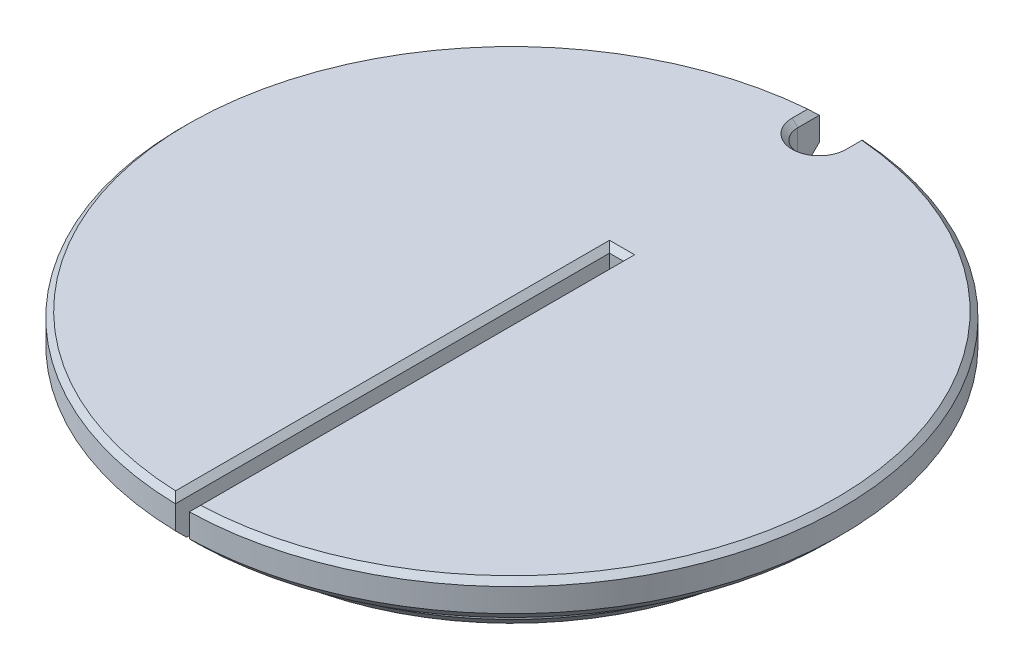
SolidWorks part; units mm, degrees
material "ABS"
ref_plane "Front Plane" through (0, 0, 0) normal (0, 0, 1) x (1, 0, 0)
ref_plane "Top Plane" through (0, 0, 0) normal (0, 1, 0) x (1, 0, 0)
ref_plane "Right Plane" through (0, 0, 0) normal (1, 0, 0) x (0, 0, -1)
sketch "Sketch1" plane through (0, 0, 0) normal (0, 0, 1) x (1, 0, 0)
  line L0 (0, -1000) -> (0, 49000) construction
  line L1 (0, 0) -> (0, -7.62)
  line L2 (0, -7.62) -> (25.0698, -7.62)
  line L3 (25.0698, -7.62) -> (25.0698, -3.6576)
  line L4 (25.0698, -3.6576) -> (30.0228, -3.6576)
  line L5 (30.0228, -3.6576) -> (30.0228, 0)
  line L6 (30.0228, 0) -> (0, 0)
  dimension "D1" = 30.0228
  dimension "D2" = 25.0698
  dimension "D3" = 7.62
  dimension "D4" = 3.6576
revolve "Revolve1" add sketch "Sketch1" angle 360 about L0
sketch "Sketch3" plane through (0, 0, 0) normal (0, 1, 0) x (1, 0, 0)
  line L0 (-0.635, 9.525) -> (0.635, 9.525)
  line L1 (0.635, 9.525) -> (0.635, -30.0161)
  line L2 (-0.635, 9.525) -> (-0.635, -30.0161)
  line L3 (0, -1000) -> (0, 49000) construction
  circle A0 centre (0, 0) radius 30.0228 construction
  arc A1 (-0.635, -30.0161) -> (0.635, -30.0161) centre (0, 0) ccw
  dimension "D1" = 9.525
  dimension "D2" = 1.27
extrude "Cut-Extrude2" cut sketch "Sketch3" against normal through all
sketch "Sketch5" plane through (0, 0, 0) normal (0, 1, 0) x (1, 0, 0)
  line L0 (0, -1000) -> (0, 49000) construction
  line L1 (-1.9558, 29.959) -> (-1.9558, 27.9908)
  line L2 (1.9558, 29.959) -> (1.9558, 27.9908)
  arc A0 (0.635, -30.0161) -> (-0.635, -30.0161) centre (0, 0) ccw construction
  arc A1 (-1.9558, 29.959) -> (1.9558, 29.959) centre (0, 0) cw
  arc A2 (-1.9558, 27.9908) -> (1.9558, 27.9908) centre (0, 27.9908) ccw
  dimension "D1" = 3.9878
  dimension "D2" = 3.9116
extrude "Cut-Extrude3" cut sketch "Sketch5" against normal through all
chamfer "Chamfer1" distance 1.016 angle 45 3 edges at (0, -7.62, -25.0698) (30.0155, -3.6576, 0.661) (-30.0155, -3.6576, 0.661)
chamfer "Chamfer2" distance 0.508 angle 45 8 edges at (30.0155, 0, 0.661) (-30.0155, 0, 0.661) (1.9558, 0, -28.9749) (0, 0, -26.035) (-1.9558, 0, -28.9749) (0.635, 0, 10.2455) (0, 0, -9.525) (-0.635, 0, 10.2455)
